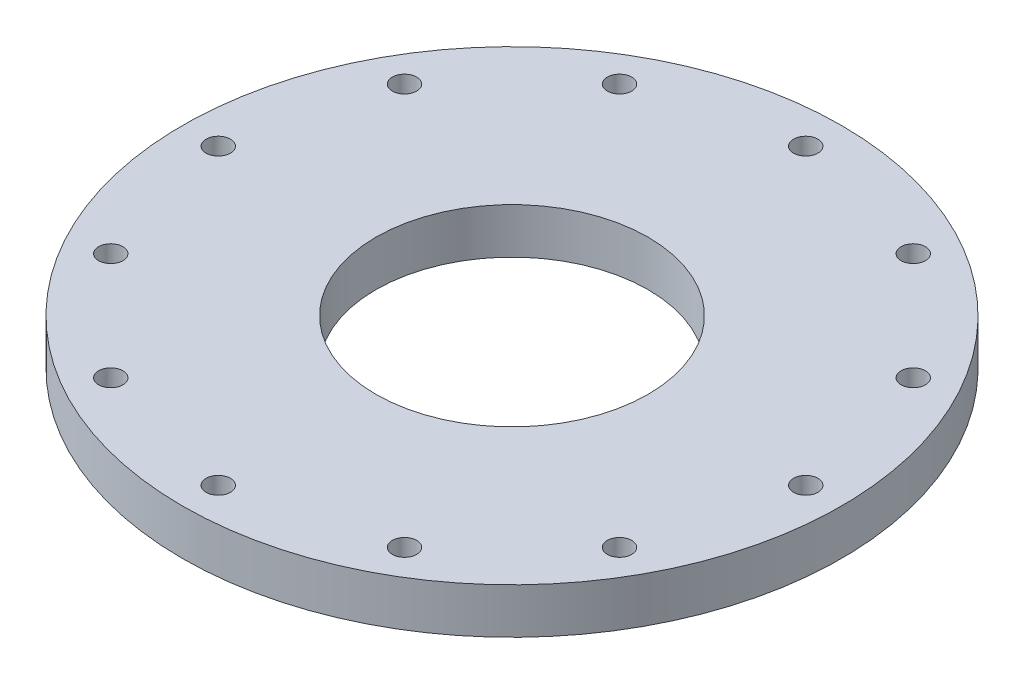
SolidWorks part; units mm, degrees
material "AISI 316 Annealed Stainless Steel Bar (SS)"
ref_plane "Front Plane" through (0, 0, 0) normal (0, 0, 1) x (1, 0, 0)
ref_plane "Top Plane" through (0, 0, 0) normal (0, 1, 0) x (1, 0, 0)
ref_plane "Right Plane" through (0, 0, 0) normal (1, 0, 0) x (0, 0, -1)
sketch "Sketch2" plane through (0, 0, 0) normal (1, 0, 0) x (0, 0, -1)
  line L0 (-19, 0) -> (-19, 6.35)
  line L1 (-19, 6.35) -> (-46, 6.35)
  line L2 (-46, 6.35) -> (-46, 0)
  line L3 (-46, 0) -> (-19, 0)
  line L4 (0, 0) -> (0, 30.9984)
  dimension "D1" = 46
  dimension "D2" = 19
  dimension "D3" = 6.35
revolve "Revolve1" add sketch "Sketch2" angle 360 about L4
sketch "Sketch3" plane through (0, 6.35, 0) normal (0, 1, 0) x (1, 0, 0)
  line L0 (0, 0) -> (0, 46)
  circle A0 centre (0, 0) radius 46 construction
  circle A1 centre (0, 41) radius 2.2058
  dimension "D1" = 5
hole_wizard "M3 Clearance Hole1" positions "Sketch5" profile "Sketch4" hole size "M3" standard "ANSI Metric" end condition through all
sketch "Sketch5" plane through (0, 6.35, 0) normal (0, 1, 0) x (1, 0, 0)
  point P0 (0, 41)
sketch "Sketch4" plane through (0, 6.35, -41) normal (1, 0, 0) x (0, 0, 1)
  line L0 (0, 0) -> (0, 6.35)
  line L1 (0, 6.35) -> (1.7, 6.35)
  line L2 (1.7, 6.35) -> (1.7, 0)
  line L5 (1.7, 0) -> (0, 0)
  line L11 (0, -6.35) -> (0, 107.95) construction
  dimension "Thru Hole Dia." = 3.4
  dimension "Thru Hole Depth" = 6.35
pattern_circular "CirPattern1" count 12 over 360 about axis through (0, 0, 0) along (0, 1, 0) of "M3 Clearance Hole1"
equation "\"r_cc_inner\"= 10'combustion chamber inner radius [mm]"
equation "\"r_cc_outer\"= 24'combustion chamber outer radius [mm]"
equation "\"L_star\"= 1500'combustion process characteristic length [mm]"
equation "\"At\"= 0.0000598 * ( 1000 ) ^ 2'Throat Area [mm^2]"
equation "\"x_cc\"= \"L_star\" * \"At\" / ( pi * ( \"r_cc_outer\" ^ 2 - \"r_cc_inner\" ^ 2 ) )'combustion chamber physical length [mm]"
equation "\"x_convergent\"= 20'length of the convergent section of the nozzle [mm]"
equation "\"r_throat\"= 15'outer radius of throat gap [mm]"
equation "\"x_material_change\"= 1.5 * \"r_throat\"'distance below throat at which nozzle material changes to a low-temp material [mm]"
equation "\"t_i\"= 8'insulation thickness required by thermal considerations [mm]"
equation "\"t_cw\"= 4'pressure vessle cylinder wall thickness required by structural considerations [mm]"
equation "\"t_p\" = 1 / 4 * 25.4'pressure vessle plate thickness required by structural considerations [mm]"
equation "\"r_outer\"= \"r_cc_outer\" + \"t_i\" + \"t_cw\" + 10'overall outermost radius of engine [mm]"
equation "\"r_rod\"= 1 / 8 * 25.4 / 2'radius of the threaded rod in the center fo the spike [mm]"
equation "\"D1@Sketch2\" = \"r_outer\""
equation "\"D2@Sketch2\"=\"r_throat\"+\"t_i\"/2"
equation "\"D3@Sketch2\"=\"t_p\""
